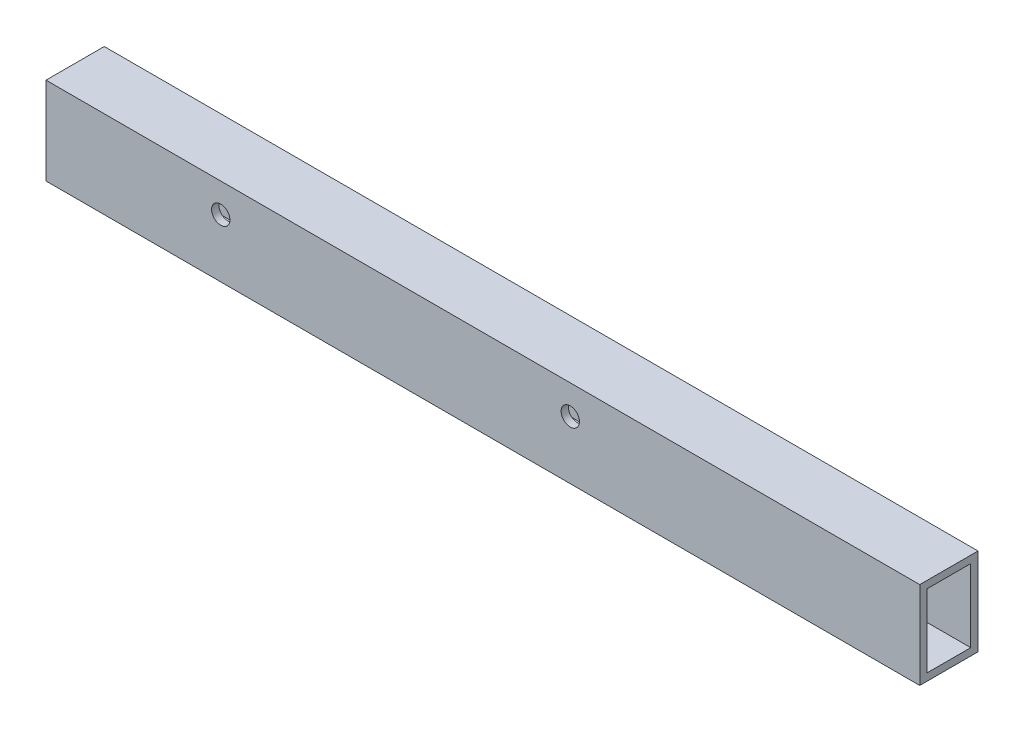
SolidWorks part; units mm, degrees
ref_plane "Front Plane" through (0, 0, 0) normal (0, 0, 1) x (1, 0, 0)
ref_plane "Top Plane" through (0, 0, 0) normal (0, 1, 0) x (1, 0, 0)
ref_plane "Right Plane" through (0, 0, 0) normal (1, 0, 0) x (0, 0, -1)
sketch "Sketch1" plane through (0, 0, 0) normal (1, 0, 0) x (0, 0, -1)
  line L0 (-9.525, -15.875) -> (-9.525, 15.875)
  line L1 (-12.7, -19.05) -> (12.7, -19.05)
  line L2 (-12.7, -19.05) -> (-12.7, 19.05)
  line L3 (-12.7, 19.05) -> (12.7, 19.05)
  line L4 (12.7, -19.05) -> (12.7, 19.05)
  line L5 (-12.7, -19.05) -> (12.7, 19.05) construction
  line L6 (-12.7, 19.05) -> (12.7, -19.05) construction
  line L7 (-9.525, 15.875) -> (9.525, 15.875)
  line L8 (9.525, -15.875) -> (9.525, 15.875)
  line L9 (-9.525, -15.875) -> (9.525, -15.875)
  point P0 (0, 0)
  dimension "D1" = 25.4
  dimension "D2" = 38.1
  dimension "D3" = 3.175
extrude "Boss-Extrude1" add sketch "Sketch1" along normal blind 381
sketch "Sketch2" plane through (0, 0, -12.7) normal (0, 0, -1) x (-1, 0, 0)
  line L0 (-381, 19.05) -> (0, 19.05) construction
  line L1 (0, -19.05) -> (0, 19.05) construction
  line L2 (-76.2, 6.35) -> (-228.6, 6.35) construction
  circle A0 centre (-76.2, 6.35) radius 4
  circle A1 centre (-228.6, 6.35) radius 4
  dimension "D1" = 8
  dimension "D2" = 12.7
  dimension "D3" = 76.2
  dimension "D4" = 152.4
extrude "Cut-Extrude1" cut sketch "Sketch2" against normal through all
